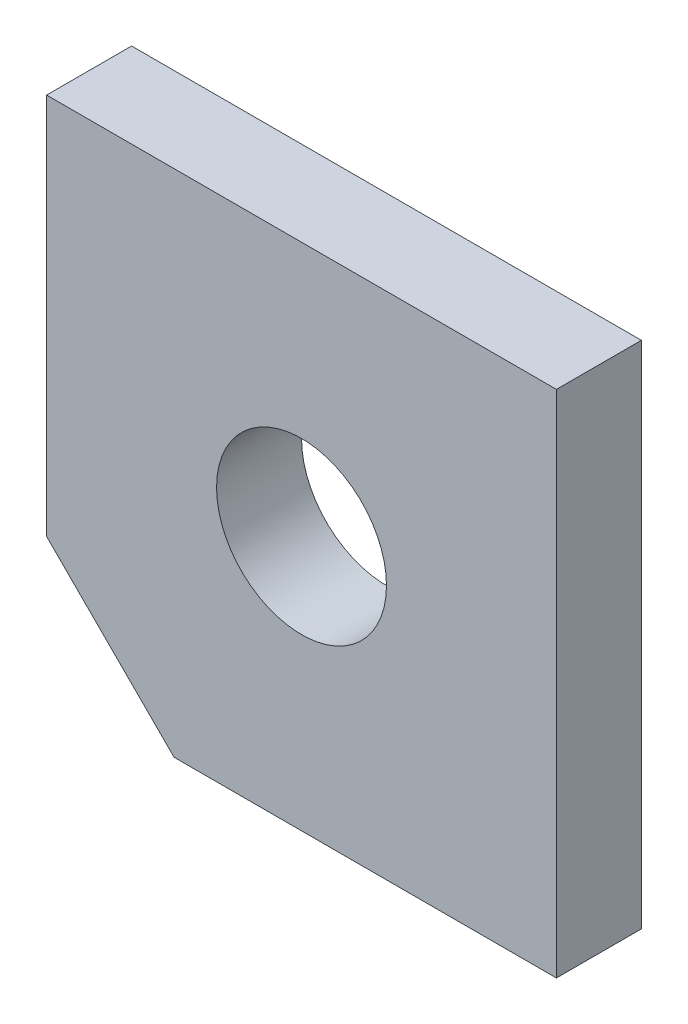
SolidWorks part; units mm, degrees
ref_plane "Front Plane" through (0, 0, 0) normal (0, 0, 1) x (1, 0, 0)
ref_plane "Top Plane" through (0, 0, 0) normal (0, 1, 0) x (1, 0, 0)
ref_plane "Right Plane" through (0, 0, 0) normal (1, 0, 0) x (0, 0, -1)
sketch "Sketch1" plane through (0, 0, 0) normal (0, 0, 1) x (1, 0, 0)
  line L0 (-38.1, 0) -> (-38.1, 76.2) construction
  line L1 (0, 0) -> (-76.2, 0)
  line L2 (0, 0) -> (0, 76.2)
  line L3 (0, 76.2) -> (-76.2, 76.2)
  line L4 (-76.2, 0) -> (-76.2, 76.2)
  line L5 (0, 38.1) -> (-76.2, 38.1) construction
  circle A0 centre (-38.1, 38.1) radius 12.7
  dimension "D3" = 25.4
  dimension "D1" = 76.2
  dimension "D2" = 76.2
extrude "Boss-Extrude1" add sketch "Sketch1" along normal blind 12.7
chamfer "Chamfer1" distance 19.05 angle 45 1 edges at (-76.2, 0, 6.35)
